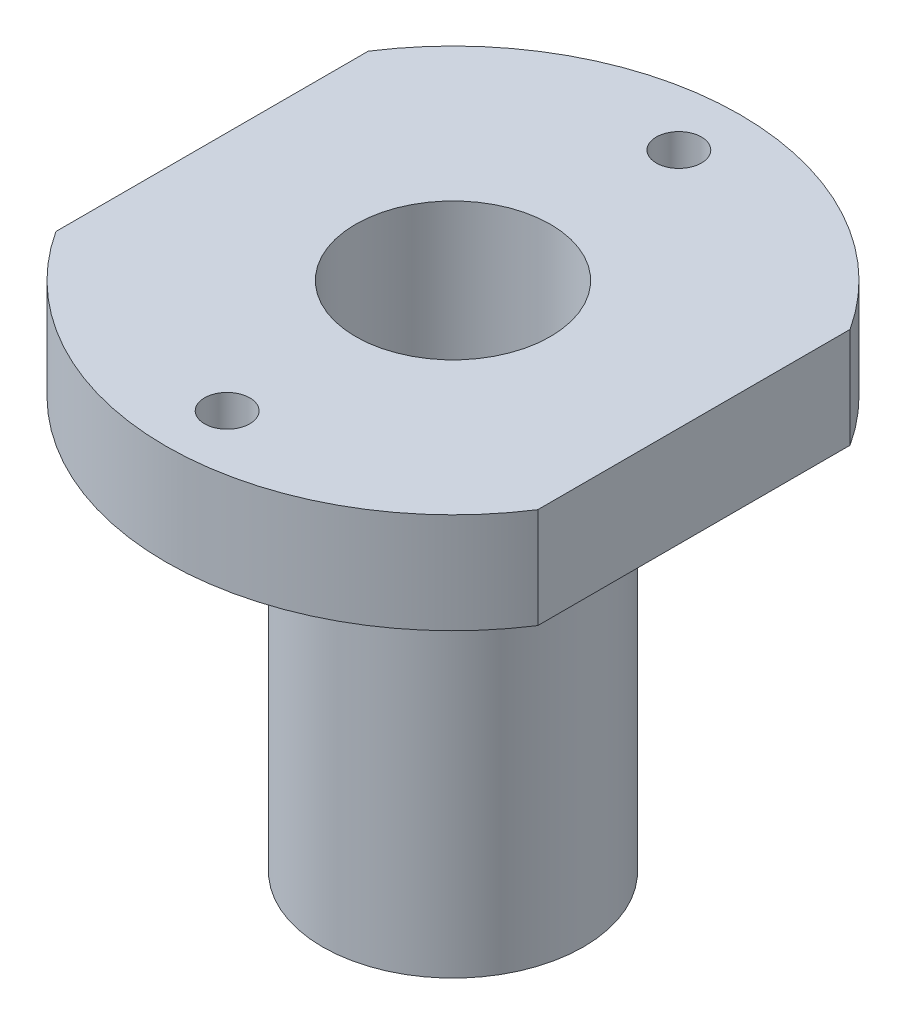
SolidWorks part; units mm, degrees
ref_plane "Plan de face" through (0, 0, 0) normal (0, 0, 1) x (1, 0, 0)
ref_plane "Plan de dessus" through (0, 0, 0) normal (0, 1, 0) x (1, 0, 0)
ref_plane "Plan de droite" through (0, 0, 0) normal (1, 0, 0) x (0, 0, -1)
sketch "Sketch1" plane through (0, 0, 0) normal (0, 1, 0) x (1, 0, 0)
  circle A0 centre (0, 0) radius 14.3
  dimension "D1" = 28.6
extrude "Boss-Extrude1" add sketch "Sketch1" along normal blind 5
sketch "Sketch2" plane through (0, 0, 0) normal (0, -1, 0) x (1, 0, 0)
  circle A0 centre (0, 0) radius 6.5
  dimension "D1" = 13
extrude "Boss-Extrude2" add sketch "Sketch2" along normal blind 20.5
sketch "Sketch5" plane through (0, 5, 0) normal (0, 1, 0) x (1, 0, 0)
  line L1 (0, -14.3) -> (0, 14.3) construction
  line L2 (0, 0) -> (-8.079, 0) construction
  circle A0 centre (0, -11.25) radius 1.125
  circle A1 centre (0, 11.25) radius 1.125
  circle A2 centre (0, 0) radius 14.3 construction
  dimension "D1" = 2.25
  dimension "D2" = 2.25
  dimension "D4" = 11.25
  dimension "D3" = 11.25
extrude "Cut-Extrude1" cut sketch "Sketch5" against normal blind 15
sketch "Sketch6" plane through (0, -20.5, 0) normal (0, -1, 0) x (1, 0, 0)
  circle A0 centre (0, 0) radius 4.85
  dimension "D1" = 9.7
extrude "Cut-Extrude2" cut sketch "Sketch6" against normal up to surface (25.5 mm away) up to face at (0, 5, -10.125)
sketch "Sketch7" plane through (0, 5, 0) normal (0, 1, 0) x (1, 0, 0)
  line L1 (12, 16.9421) -> (-12, 16.9421) construction
  line L2 (12, 16.9421) -> (12, -15.4053)
  line L3 (12, -15.4053) -> (-12, -15.4053) construction
  line L4 (-12, 16.9421) -> (-12, -15.4053)
  line L5 (12, 16.9421) -> (15.2635, 16.9421)
  line L6 (12, 16.9421) -> (12, -15.4053)
  line L7 (12, -15.4053) -> (15.2635, -15.4053)
  line L8 (15.2635, 16.9421) -> (15.2635, -15.4053)
  line L9 (-12, -15.4053) -> (-15.5283, -15.4053)
  line L10 (-12, -15.4053) -> (-12, 16.9421)
  line L11 (-12, 16.9421) -> (-15.5283, 16.9421)
  line L12 (-15.5283, -15.4053) -> (-15.5283, 16.9421)
  circle M7 centre (0, 0) radius 14.3
  dimension "D1" = 12
  dimension "D2" = 24
extrude "Cut-Extrude5" cut sketch "Sketch7" against normal blind 10 contours L8 L5 L2 L7 M7 | L12 L9 L4 L11 M7 | L2 M7 | L4 M7
